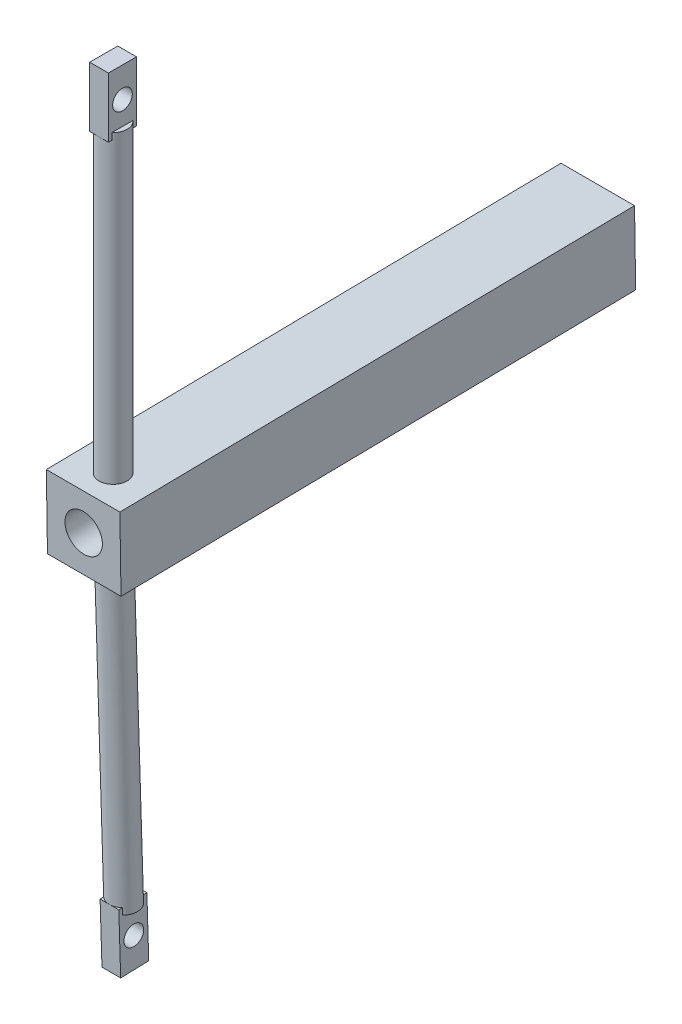
SolidWorks part; units mm, degrees
ref_plane "Front Plane" through (0, 0, 0) normal (0, 0, 1) x (1, 0, 0)
ref_plane "Top Plane" through (0, 0, 0) normal (0, 1, 0) x (1, 0, 0)
ref_plane "Right Plane" through (0, 0, 0) normal (1, 0, 0) x (0, 0, -1)
ref_plane "Plane3" through (0, -640.0985, 41284.1748) normal (0, -0.0155, 0.9999) x (-1, 0, 0)
sketch "Sketch1" plane through (0, 27232.8776, 41716.3367) normal (0, -0.0155, 0.9999) x (1, 0, 0)
  line L0 (-23448.047, 6519.584) -> (-23298.047, 6299.3386) construction
  line L7 (-23333.7506, 6448.7577) -> (-23412.3434, 6448.7577)
  line L8 (-23333.7506, 6448.7577) -> (-23333.7506, 6370.1649)
  line L9 (-23333.7506, 6370.1649) -> (-23412.3434, 6370.1649)
  line L10 (-23412.3434, 6448.7577) -> (-23412.3434, 6370.1649)
  line L11 (-23333.7506, 6448.7577) -> (-23412.3434, 6370.1649) construction
  line L12 (-23333.7506, 6370.1649) -> (-23412.3434, 6448.7577) construction
  line L13 (-23448.047, 6299.3386) -> (-23298.047, 6519.584) construction
  circle A0 centre (-23373.047, 6409.4613) radius 20
  dimension "D1" = 40
extrude "Boss-Extrude4" add sketch "Sketch1" against normal blind 550
sketch3d "3DSketch2"
  line L0 (-23580.8189, 34031.8953, 41784.2489) -> (-23067.6878, 34031.8953, 41784.2489) construction
  line L1 (-23155.8189, 34031.8953, 41784.2489) -> (-23580.8189, 34031.8953, 41784.2489) construction
  line L2 (-23373.047, 34031.8953, 41784.2489) -> (-23373.047, 33650.0952, 41784.2489) construction
  line L3 (-23373.047, 33650.0952, 41265.7676) -> (-23373.047, 33650.0952, 41784.2489) construction
  line L4 (-23373.047, 33650.0952, 41265.7676) -> (-23373.047, 33641.5687, 41815.7015) construction
  line L5 (-23373.047, 33650.0952, 41784.2489) -> (-23373.047, 33276.9983, 41784.2489) construction
  line L6 (-23580.8189, 33251.9891, 41772.1567) -> (-23307.9375, 33251.9891, 41772.1567) construction
  line L7 (-23155.8189, 33251.9891, 41772.1567) -> (-23580.8189, 33251.9891, 41772.1567) construction
  line L8 (-23373.047, 34006.8953, 41784.2489) -> (-23373.047, 33681.3574, 41784.2489)
  dimension "D1" = 25
sweep "Sweep1" add path "3DSketch2" circular profile diameter 30 parameters "D3"=30
ref_plane "Plane4" through (-23373.047, 0, 0) normal (-1, 0, 0) x (0, 0, 1)
sketch "Sketch15" plane through (-23373.047, 0, 0) normal (-1, 0, 0) x (0, 0, 1)
  line L0 (41769.2489, 34006.8953) -> (41769.2489, 33681.59) construction
  line L1 (41769.2489, 34063.9324) -> (41799.2489, 34063.9324)
  line L2 (41769.2489, 34063.9324) -> (41769.2489, 33999.8583)
  line L3 (41769.2489, 33999.8583) -> (41799.2489, 33999.8583)
  line L4 (41799.2489, 34063.9324) -> (41799.2489, 33999.8583)
  line L5 (41769.2489, 34063.9324) -> (41799.2489, 33999.8583) construction
  line L6 (41769.2489, 33999.8583) -> (41799.2489, 34063.9324) construction
  line L7 (41799.2489, 33681.3574) -> (41799.2489, 34006.8953) construction
  circle A0 centre (41784.2489, 34031.8953) radius 10.5
  circle A1 centre (41784.2489, 34031.8953) radius 10 construction
  point P0 (41784.2489, 34031.8953)
  dimension "D1" = 21
extrude "Boss-Extrude5" add sketch "Sketch15" along normal blind 10 and the other way blind 10
ref_plane "Plane5" through (0, 34281.6671, 531.5267) normal (0, -0.9999, -0.0155) x (-1, 0, 0)
mirror "Mirror1" about plane through (0, 34281.6671, 531.5267) normal (0, -0.9999, -0.0155) of "Boss-Extrude5", "Sweep1"
